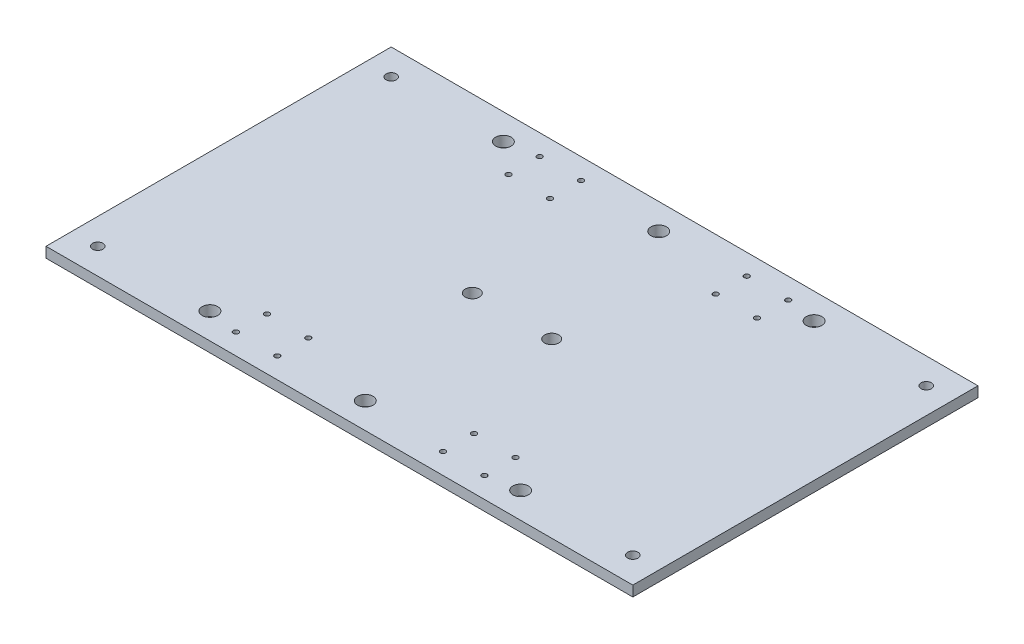
SolidWorks part; units mm, degrees
material "Acrylic (Medium-high impact)"
ref_plane "Front Plane" through (0, 0, 0) normal (0, 0, 1) x (1, 0, 0)
ref_plane "Top Plane" through (0, 0, 0) normal (0, 1, 0) x (1, 0, 0)
ref_plane "Right Plane" through (0, 0, 0) normal (1, 0, 0) x (0, 0, -1)
sketch "Sketch1" plane through (0, 0, 0) normal (0, 1, 0) x (1, 0, 0)
  line L0 (-1000, 0) -> (49000, 0) construction
  line L1 (-170, 100) -> (170, 100)
  line L2 (-170, 100) -> (-170, -100)
  line L3 (-170, -100) -> (170, -100)
  line L4 (170, 100) -> (170, -100)
  line L5 (-170, 100) -> (170, -100) construction
  line L6 (-170, -100) -> (170, 100) construction
  line L7 (0, -1000) -> (0, 49000) construction
  line L8 (60, -1000) -> (60, 49000) construction
  line L9 (-60, -1000) -> (-60, 49000) construction
  line L11 (48, 88) -> (72, 88) construction
  line L12 (48, 88) -> (48, 70) construction
  line L13 (48, 70) -> (72, 70) construction
  line L14 (72, 88) -> (72, 70) construction
  line L15 (48, 88) -> (72, 70) construction
  line L16 (48, 70) -> (72, 88) construction
  circle A0 centre (-23, 0) radius 4.1
  circle A1 centre (23, 0) radius 4.1
  circle A2 centre (72, 88) radius 1.5
  circle A3 centre (48, 88) radius 1.5
  circle A4 centre (72, 70) radius 1.5
  circle A5 centre (48, 70) radius 1.5
  circle A6 centre (-48, 70) radius 1.5
  circle A7 centre (-72, 70) radius 1.5
  circle A8 centre (-48, 88) radius 1.5
  circle A9 centre (-72, 88) radius 1.5
  circle A10 centre (-72, -88) radius 1.5
  circle A11 centre (-48, -88) radius 1.5
  circle A12 centre (-72, -70) radius 1.5
  circle A13 centre (-48, -70) radius 1.5
  circle A14 centre (48, -70) radius 1.5
  circle A15 centre (72, -70) radius 1.5
  circle A16 centre (48, -88) radius 1.5
  circle A17 centre (72, -88) radius 1.5
  circle A18 centre (155, 85) radius 3
  circle A19 centre (-155, 85) radius 3
  circle A20 centre (155, -85) radius 3
  circle A21 centre (-155, -85) radius 3
  circle A23 centre (0, 85) radius 4.5
  circle A24 centre (0, -85) radius 4.5
  circle A25 centre (90, 85) radius 4.5
  circle A26 centre (90, -85) radius 4.5
  circle A27 centre (-90, -85) radius 4.5
  circle A28 centre (-90, 85) radius 4.5
  point P0 (0, 0)
  point P18 (60, 79)
  dimension "D5" = 8.2
  dimension "D6" = 23
  dimension "D10" = 3
  dimension "D12" = 18
  dimension "D15" = 6
  dimension "D16" = 9
  dimension "D17" = 15
  dimension "D19" = 90
  dimension "D1" = 200
  dimension "D2" = 340
  dimension "D7" = 24
  dimension "D8" = 18
  dimension "D9" = 70
  dimension "D13" = 15
  dimension "D14" = 15
  dimension "D3" = 60
  dimension "D4" = 60
  dimension "D11" = 2
  dimension "D18" = 2
extrude "Boss-Extrude1" add sketch "Sketch1" along normal blind 6
sketch "Sketch2" plane through (0, 6, 0) normal (0, 1, 0) x (1, 0, 0)
  line L0 (0, -1000) -> (0, 49000) construction
  line L1 (-1000, 0) -> (49000, 0) construction
  circle A0 centre (72, 88) radius 2.5
  circle A1 centre (48, 88) radius 2.5
  circle A2 centre (48, 70) radius 2.5
  circle A3 centre (72, 70) radius 2.5
  circle A5 centre (-72, 70) radius 2.5
  circle A6 centre (-48, 70) radius 2.5
  circle A7 centre (-48, 88) radius 2.5
  circle A8 centre (-72, 88) radius 2.5
  circle A9 centre (-72, -88) radius 2.5
  circle A10 centre (-48, -88) radius 2.5
  circle A11 centre (-48, -70) radius 2.5
  circle A12 centre (-72, -70) radius 2.5
  circle A13 centre (72, -70) radius 2.5
  circle A14 centre (48, -70) radius 2.5
  circle A15 centre (48, -88) radius 2.5
  circle A16 centre (72, -88) radius 2.5
  circle A17 centre (23, 0) radius 5.5
  circle A19 centre (-23, 0) radius 5.5
  circle A20 centre (0, 85) radius 10
  circle A21 centre (0, -85) radius 10
  circle A22 centre (90, 85) radius 10
  circle A23 centre (90, -85) radius 10
  circle A24 centre (-90, -85) radius 10
  circle A25 centre (-90, 85) radius 10
  dimension "D1" = 5
  dimension "D7" = 11
  dimension "D8" = 20
  dimension "D10" = 90
  dimension "D4" = 18
  dimension "D5" = 24
  dimension "D6" = 30
  dimension "D2" = 2
  dimension "D3" = 2
  dimension "D9" = 2
extrude "Cut-Extrude1" [suppressed] cut sketch "Sketch2" against normal blind 3
